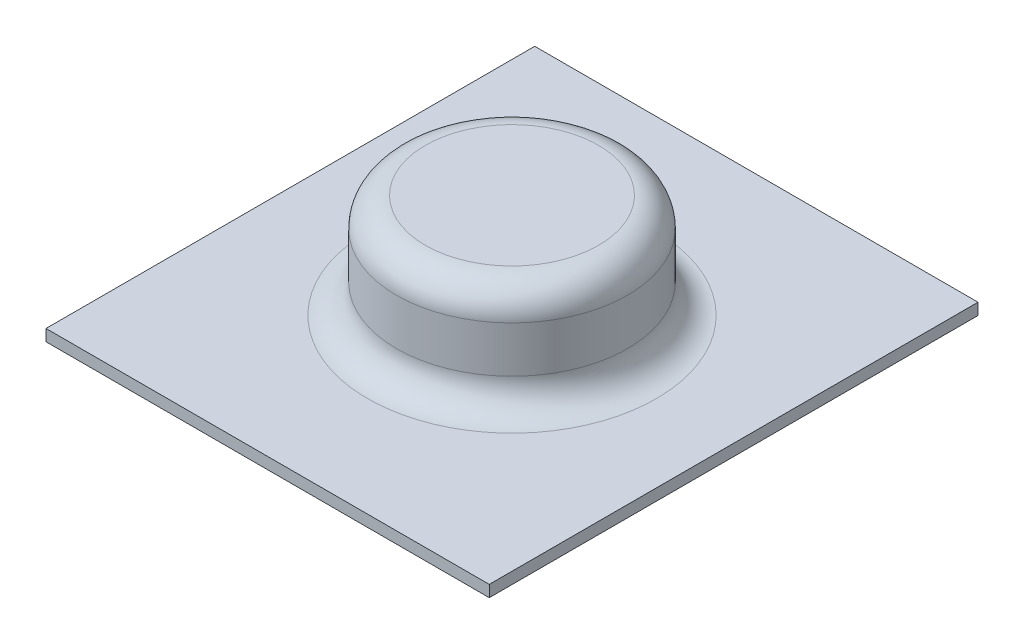
SolidWorks part; units mm, degrees
ref_plane "Front Plane" through (0, 0, 0) normal (0, 0, 1) x (1, 0, 0)
ref_plane "Top Plane" through (0, 0, 0) normal (0, 1, 0) x (1, 0, 0)
ref_plane "Right Plane" through (0, 0, 0) normal (1, 0, 0) x (0, 0, -1)
sketch "Sketch1" plane through (0, 0, 0) normal (0, 1, 0) x (1, 0, 0)
  line L1 (9.75, 10.75) -> (-9.75, 10.75)
  line L2 (9.75, 10.75) -> (9.75, -10.75)
  line L3 (9.75, -10.75) -> (-9.75, -10.75)
  line L4 (-9.75, 10.75) -> (-9.75, -10.75)
  line L5 (9.75, 10.75) -> (-9.75, -10.75) construction
  line L6 (9.75, -10.75) -> (-9.75, 10.75) construction
  point P0 (0, 0)
  dimension "D1" = 21.5
  dimension "D2" = 19.5
extrude "Boss-Extrude1" add sketch "Sketch1" along normal blind 0.508
sketch "Sketch2" plane through (0, 0, 0) normal (0, 1, 0) x (1, 0, 0)
  circle A0 centre (0, 0) radius 5.08
  dimension "D1" = 10.16
extrude "Boss-Extrude2" add sketch "Sketch2" along normal blind 5.08
fillet "Fillet1" radius 1.27 2 edges at (0, 0.508, -5.08) (0, 5.08, 5.08)
